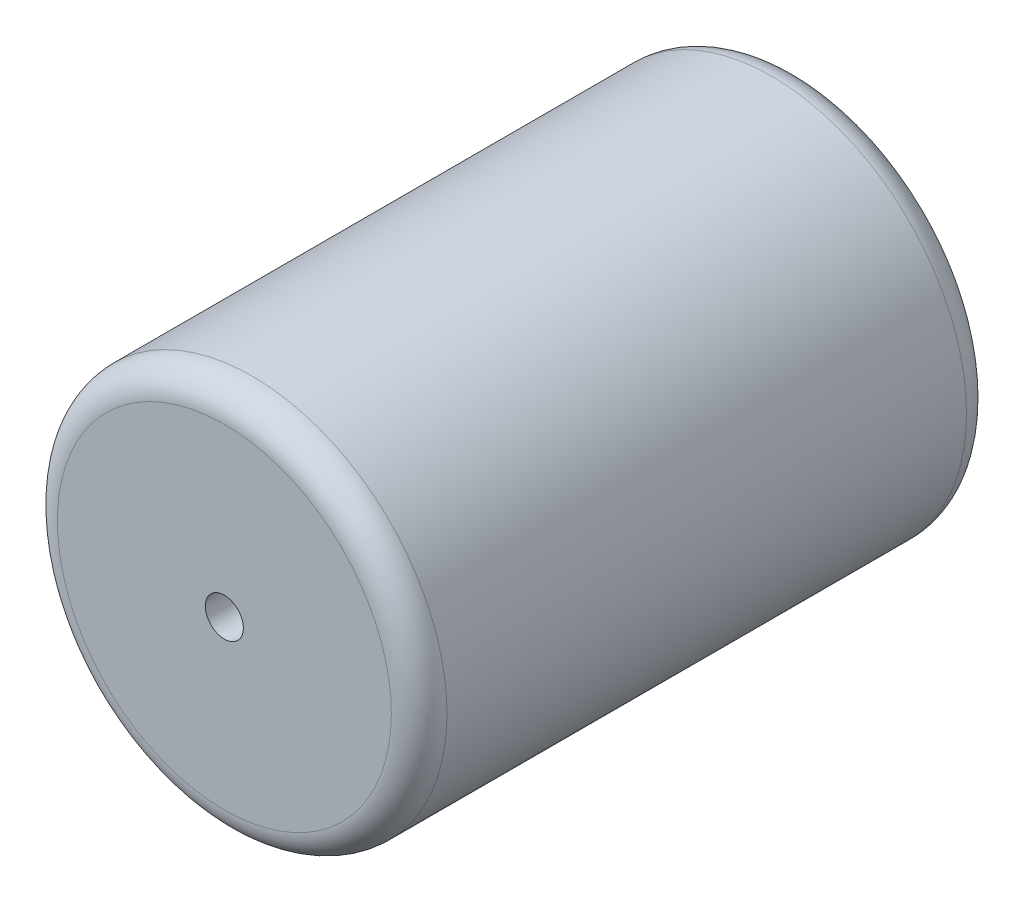
SolidWorks part; units mm, degrees
ref_plane "Front Plane" through (0, 0, 0) normal (0, 0, 1) x (1, 0, 0)
ref_plane "Top Plane" through (0, 0, 0) normal (0, 1, 0) x (1, 0, 0)
ref_plane "Right Plane" through (0, 0, 0) normal (1, 0, 0) x (0, 0, -1)
sketch "Sketch1" plane through (0, 0, 0) normal (0, 0, 1) x (1, 0, 0)
  circle A0 centre (0, 0) radius 10.5
  dimension "D1" = 21
extrude "Boss-Extrude1" add sketch "Sketch1" along normal blind 31
fillet "Fillet1" radius 1.5 2 edges at (10.5, 0, 0) (10.5, 0, 31)
sketch "Sketch2" plane through (0, 0, 0) normal (0, 0, -1) x (-1, 0, 0)
  circle A0 centre (0, 0) radius 1.025
  dimension "D1" = 2.05
extrude "Cut-Extrude1" cut sketch "Sketch2" against normal blind 35
